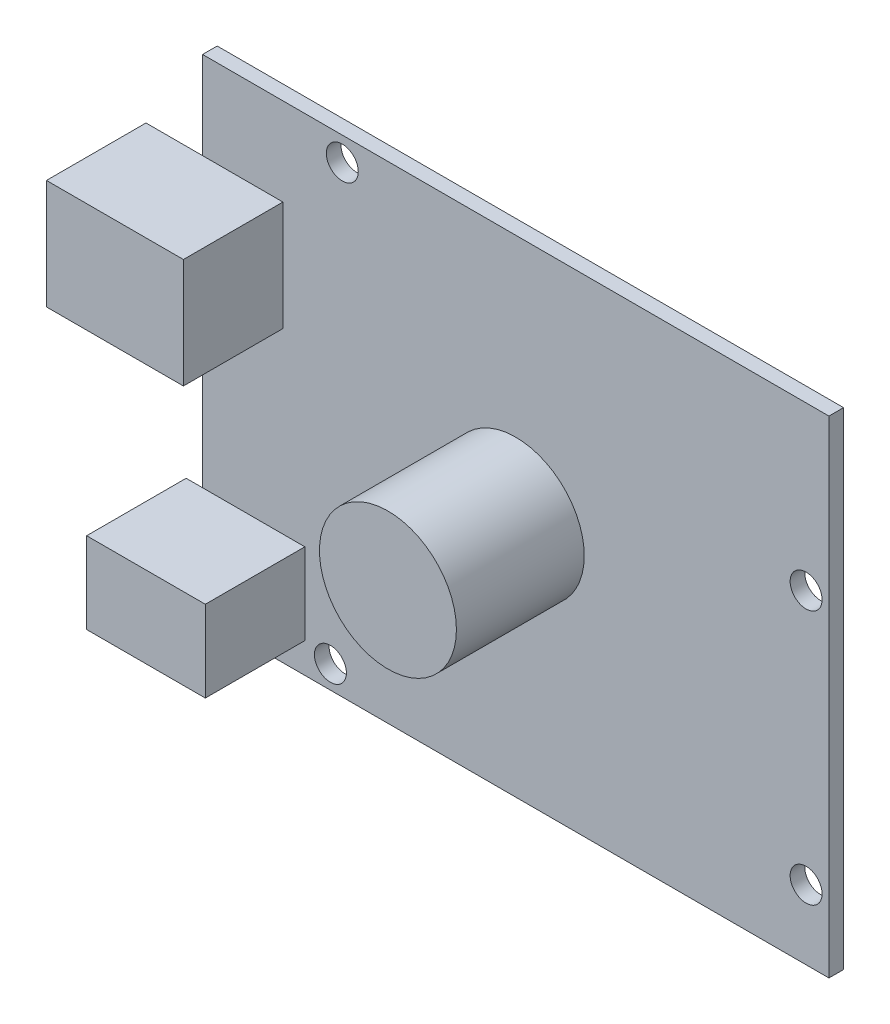
SolidWorks part; units mm, degrees
ref_plane "Front Plane" through (0, 0, 0) normal (0, 0, 1) x (1, 0, 0)
ref_plane "Top Plane" through (0, 0, 0) normal (0, 1, 0) x (1, 0, 0)
ref_plane "Right Plane" through (0, 0, 0) normal (1, 0, 0) x (0, 0, -1)
sketch "Sketch1" plane through (0, 0, 0) normal (0, 0, 1) x (1, 0, 0)
  line L1 (-34.3, 26.65) -> (34.3, 26.65)
  line L2 (-34.3, 26.65) -> (-34.3, -26.65)
  line L3 (-34.3, -26.65) -> (34.3, -26.65)
  line L4 (34.3, 26.65) -> (34.3, -26.65)
  point P4 (0, 26.65)
  point P6 (-34.3, 0)
  dimension "D1" = 68.6
  dimension "D2" = 53.3
extrude "Boss-Extrude1" add sketch "Sketch1" along normal blind 1.6
sketch "Sketch2" plane through (0, 0, 1.6) normal (0, 0, 1) x (1, 0, 0)
  line L0 (-34.3, 26.65) -> (-34.3, -26.65) construction
  line L1 (-40.5, 17.05) -> (-25.5, 17.05)
  line L2 (-40.5, 17.05) -> (-40.5, 5.05)
  line L3 (-40.5, 5.05) -> (-25.5, 5.05)
  line L4 (-25.5, 17.05) -> (-25.5, 5.05)
  line L5 (-36.1, -14.45) -> (-23.1, -14.45)
  line L6 (-36.1, -14.45) -> (-36.1, -23.35)
  line L7 (-36.1, -23.35) -> (-23.1, -23.35)
  line L8 (-23.1, -14.45) -> (-23.1, -23.35)
  line L9 (34.3, 26.65) -> (-34.3, 26.65) construction
  line L10 (-34.3, -26.65) -> (34.3, -26.65) construction
  dimension "D1" = 1.8
  dimension "D2" = 6.2
  dimension "D3" = 9.6
  dimension "D4" = 12
  dimension "D5" = 8.9
  dimension "D6" = 3.3
  dimension "D7" = 13
  dimension "D8" = 15
extrude "Boss-Extrude2" add sketch "Sketch2" along normal blind 10.9
sketch "Sketch3" plane through (0, 0, 1.6) normal (0, 0, 1) x (1, 0, 0)
  line L0 (-34.3, -26.65) -> (34.3, -26.65) construction
  line L1 (-34.3, 26.65) -> (-34.3, 17.05) construction
  circle A0 centre (-19, 24.05) radius 1.75
  circle A1 centre (-20.3, -24.15) radius 1.75
  circle A2 centre (31.8, -19.05) radius 1.75
  circle A3 centre (31.8, 8.85) radius 1.75
  dimension "D7" = 3.5
  dimension "D1" = 27.9
  dimension "D2" = 50.8
  dimension "D3" = 1.3
  dimension "D4" = 15.2
  dimension "D5" = 2.5
  dimension "D6" = 5.1
  dimension "D8" = 14
extrude "Cut-Extrude1" cut sketch "Sketch3" against normal through all
sketch "Sketch4" plane through (0, 0, 1.6) normal (0, 0, 1) x (1, 0, 0)
  circle A0 centre (0, 0) radius 7.5
  dimension "D1" = 15
extrude "Boss-Extrude3" add sketch "Sketch4" along normal blind 14
